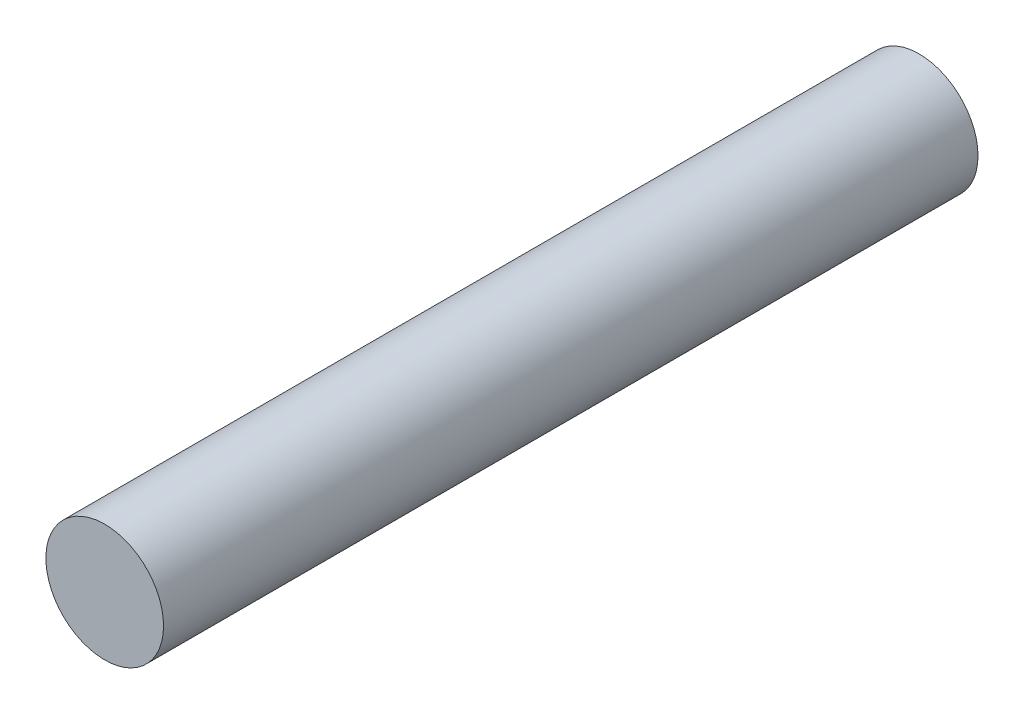
SolidWorks part; units mm, degrees
material "PA Type 6"
ref_plane "Front Plane" through (0, 0, 0) normal (0, 0, 1) x (1, 0, 0)
ref_plane "Top Plane" through (0, 0, 0) normal (0, 1, 0) x (1, 0, 0)
ref_plane "Right Plane" through (0, 0, 0) normal (1, 0, 0) x (0, 0, -1)
sketch "Sketch1" plane through (0, 0, 0) normal (0, 0, 1) x (1, 0, 0)
  circle A0 centre (0, 0) radius 6.5
  dimension "D1" = 13
extrude "Boss-Extrude1" add sketch "Sketch1" along normal mid plane 90
